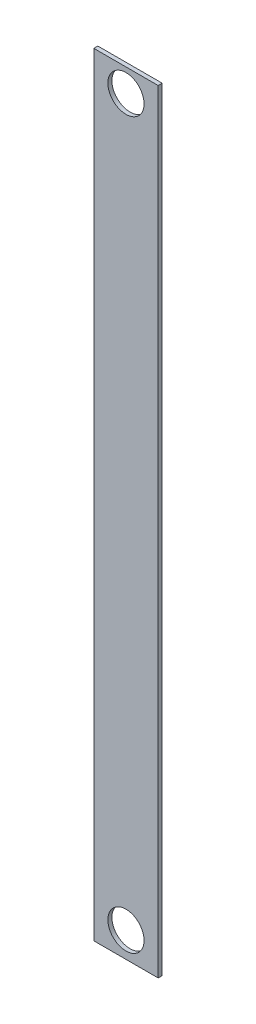
SolidWorks part; units mm, degrees
ref_plane "Front Plane" through (0, 0, 0) normal (0, 0, 1) x (1, 0, 0)
ref_plane "Top Plane" through (0, 0, 0) normal (0, 1, 0) x (1, 0, 0)
ref_plane "Right Plane" through (0, 0, 0) normal (1, 0, 0) x (0, 0, -1)
sketch "Sketch1" plane through (0, 0, 0) normal (0, 0, 1) x (1, 0, 0)
  line L1 (0, 0) -> (50.8, 0)
  line L2 (0, 0) -> (0, -609.6)
  line L3 (0, -609.6) -> (50.8, -609.6)
  line L4 (50.8, 0) -> (50.8, -609.6)
  dimension "D1" = 609.6
  dimension "D2" = 50.8
extrude "Boss-Extrude1" add sketch "Sketch1" along normal blind 3.175
sketch "Sketch2" plane through (0, 0, 3.175) normal (0, 0, 1) x (1, 0, 0)
  line L1 (50.8, 0) -> (0, 0) construction
  line L3 (0, -609.6) -> (50.8, -609.6) construction
  circle A0 centre (25.4, -18.1414) radius 14.279
  circle A1 centre (25.4, -589.6) radius 14.279
  point P3 (0, 0)
  point P6 (25.4, 0)
  point P7 (0, 0)
  dimension "D1" = 28.558
  dimension "D2" = 28.558
  dimension "D3" = 20
extrude "Cut-Extrude1" cut sketch "Sketch2" against normal through all
